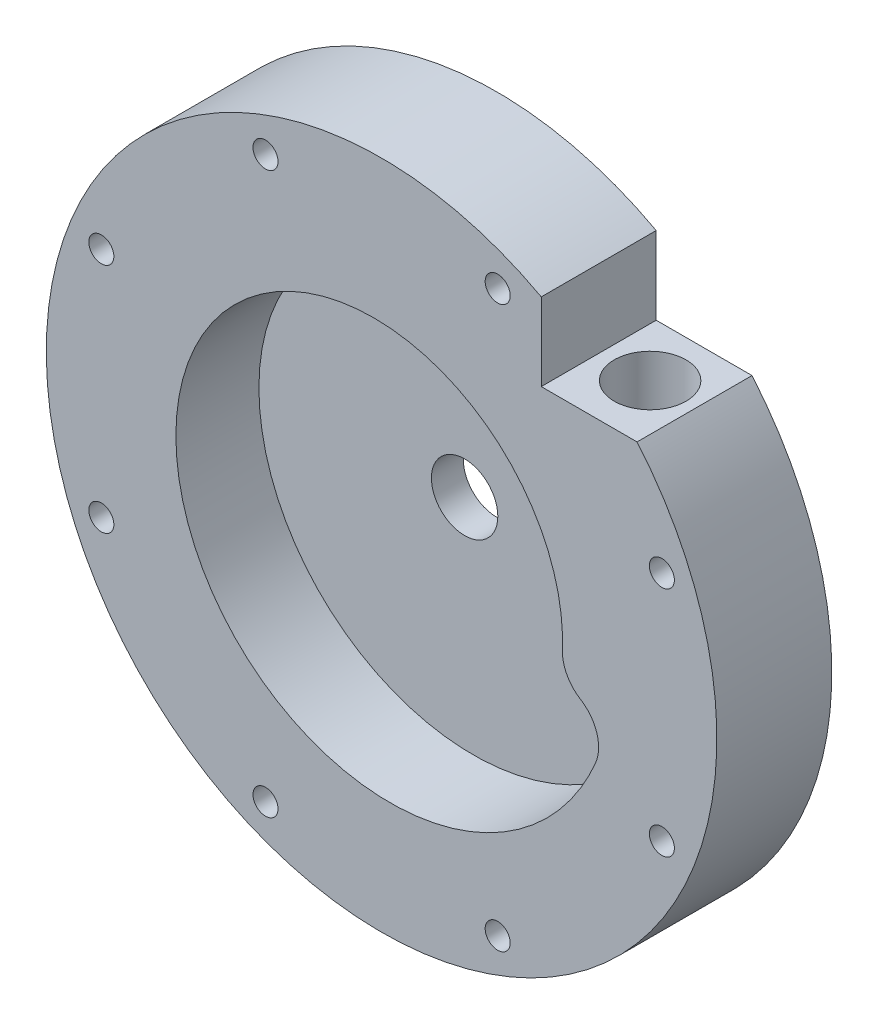
SolidWorks part; units mm, degrees
material "6061-T6 (SS)"
ref_plane "Front Plane" through (0, 0, 0) normal (0, 0, 1) x (1, 0, 0)
ref_plane "Top Plane" through (0, 0, 0) normal (0, 1, 0) x (1, 0, 0)
ref_plane "Right Plane" through (0, 0, 0) normal (1, 0, 0) x (0, 0, -1)
sketch "Sketch22" plane through (0, 0, 0) normal (0, 1, 0) x (1, 0, 0)
  line L0 (-25.4, 0) -> (-6.604, 0)
  line L1 (-25.4, 0) -> (-25.4, -16.51)
  line L2 (-17.4625, 6.35) -> (-17.4625, 3.175)
  line L3 (-25.4, -16.51) -> (-66.675, -16.51)
  line L4 (-66.675, -16.51) -> (-66.675, 6.35)
  line L9 (-17.4625, 6.35) -> (-66.675, 6.35)
  line L10 (0, 0) -> (0, 9.525) construction
  line L11 (-6.604, 6.35) -> (-6.604, 0)
  line L12 (-17.4625, 3.175) -> (-11.1125, 3.175)
  line L15 (-11.1125, 3.175) -> (-11.1125, 6.35)
  line L16 (-11.1125, 6.35) -> (-6.604, 6.35)
  line L17 (-25.4, -0.508) -> (-0.1653, -0.508) construction
  line L18 (-0.1653, -9.508) -> (-0.1653, -0.508) construction
  dimension "D5" = 50.8
  dimension "D6" = 133.35
  dimension "D7" = 13.208
  dimension "D2" = 6.35
  dimension "D4" = 22.225
  dimension "D8" = 3.175
  dimension "D1" = 6.35
  dimension "D3" = 22.86
  dimension "D9" = 0.508
revolve "Main Body" add sketch "Sketch22" angle 360 about L10
curve "Volute Spiral"
  spline degree 3 poles (35.9487, 0, 0) (35.9516, 0.0754, 0) (35.9573, 0.2262, 0) (35.9642, 0.4524, 0) (35.9698, 0.6788, 0) (35.9739, 0.9052, 0) (35.9766, 1.1318, 0) (35.9779, 1.3583, 0) (35.9778, 1.585, 0) (35.9763, 1.8117, 0) (35.9733, 2.0385, 0) (35.969, 2.2653, 0) (35.9632, 2.4921, 0) (35.956, 2.7189, 0) (35.9473, 2.9457, 0) (35.9373, 3.1726, 0) (35.9258, 3.3994, 0) (35.9129, 3.6262, 0) (35.8986, 3.853, 0) (35.8828, 4.0798, 0) (35.8656, 4.3065, 0) (35.847, 4.5331, 0) (35.827, 4.7597, 0) (35.8055, 4.9862, 0) (35.7826, 5.2127, 0) (35.7583, 5.439, 0) (35.7326, 5.6653, 0) (35.7054, 5.8914, 0) (35.6768, 6.1174, 0) (35.6468, 6.3433, 0) (35.6153, 6.5691, 0) (35.5825, 6.7947, 0) (35.5482, 7.0201, 0) (35.5124, 7.2455, 0) (35.4753, 7.4706, 0) (35.4367, 7.6955, 0) (35.3967, 7.9203, 0) (35.3553, 8.1449, 0) (35.3125, 8.3692, 0) (35.2683, 8.5934, 0) (35.2226, 8.8173, 0) (35.1755, 9.041, 0) (35.127, 9.2644, 0) (35.0771, 9.4876, 0) (35.0257, 9.7105, 0) (34.973, 9.9332, 0) (34.9188, 10.1556, 0) (34.8633, 10.3777, 0) (34.8063, 10.5995, 0) (34.7479, 10.821, 0) (34.6881, 11.0422, 0) (34.6269, 11.263, 0) (34.5643, 11.4836, 0) (34.5004, 11.7037, 0) (34.435, 11.9236, 0) (34.3682, 12.1431, 0) (34.3, 12.3622, 0) (34.2304, 12.5809, 0) (34.1594, 12.7993, 0) (34.0871, 13.0172, 0) (34.0133, 13.2348, 0) (33.9382, 13.4519, 0) (33.8617, 13.6686, 0) (33.7838, 13.8849, 0) (33.7045, 14.1008, 0) (33.6238, 14.3162, 0) (33.5418, 14.5311, 0) (33.4584, 14.7456, 0) (33.3737, 14.9596, 0) (33.2875, 15.1732, 0) (33.2, 15.3862, 0) (33.1112, 15.5988, 0) (33.021, 15.8108, 0) (32.9294, 16.0223, 0) (32.8365, 16.2333, 0) (32.7422, 16.4438, 0) (32.6466, 16.6537, 0) (32.5497, 16.8631, 0) (32.4514, 17.0719, 0) (32.3517, 17.2801, 0) (32.2508, 17.4878, 0) (32.1485, 17.6949, 0) (32.0448, 17.9013, 0) (31.9399, 18.1072, 0) (31.8336, 18.3125, 0) (31.7261, 18.5171, 0) (31.6172, 18.7212, 0) (31.507, 18.9246, 0) (31.3955, 19.1273, 0) (31.2827, 19.3294, 0) (31.1685, 19.5308, 0) (31.0531, 19.7316, 0) (30.9365, 19.9317, 0) (30.8185, 20.1311, 0) (30.6992, 20.3298, 0) (30.5787, 20.5278, 0) (30.4569, 20.7251, 0) (30.3338, 20.9217, 0) (30.2094, 21.1175, 0) (30.0838, 21.3126, 0) (29.957, 21.507, 0) (29.8288, 21.7006, 0) (29.6995, 21.8935, 0) (29.5689, 22.0856, 0) (29.437, 22.2769, 0) (29.3039, 22.4674, 0) (29.1696, 22.6571, 0) (29.0341, 22.8461, 0) (28.8973, 23.0342, 0) (28.7593, 23.2215, 0) (28.6201, 23.408, 0) (28.4797, 23.5937, 0) (28.3381, 23.7785, 0) (28.1953, 23.9625, 0) (28.0514, 24.1456, 0) (27.9062, 24.3279, 0) (27.7598, 24.5093, 0) (27.6123, 24.6898, 0) (27.4636, 24.8694, 0) (27.3137, 25.0482, 0) (27.1627, 25.226, 0) (27.0105, 25.403, 0) (26.8572, 25.579, 0) (26.7027, 25.7541, 0) (26.5471, 25.9282, 0) (26.3903, 26.1015, 0) (26.2325, 26.2738, 0) (26.0735, 26.4451, 0) (25.9134, 26.6155, 0) (25.7521, 26.7849, 0) (25.5898, 26.9533, 0) (25.4264, 27.1208, 0) (25.2619, 27.2872, 0) (25.0963, 27.4527, 0) (24.9296, 27.6172, 0) (24.7618, 27.7806, 0) (24.593, 27.9431, 0) (24.4231, 28.1045, 0) (24.2521, 28.2649, 0) (24.0802, 28.4242, 0) (23.9071, 28.5825, 0) (23.733, 28.7398, 0) (23.5579, 28.896, 0) (23.3818, 29.0511, 0) (23.2046, 29.2052, 0) (23.0265, 29.3582, 0) (22.8473, 29.5101, 0) (22.6671, 29.6609, 0) (22.486, 29.8106, 0) (22.3038, 29.9592, 0) (22.1207, 30.1067, 0) (21.9366, 30.2531, 0) (21.7515, 30.3984, 0) (21.5655, 30.5425, 0) (21.3785, 30.6855, 0) (21.1906, 30.8274, 0) (21.0018, 30.9681, 0) (20.812, 31.1076, 0) (20.6213, 31.246, 0) (20.4297, 31.3833, 0) (20.2371, 31.5193, 0) (20.0437, 31.6542, 0) (19.8494, 31.7879, 0) (19.6541, 31.9204, 0) (19.458, 32.0517, 0) (19.2611, 32.1818, 0) (19.0632, 32.3106, 0) (18.8645, 32.4383, 0) (18.665, 32.5648, 0) (18.4646, 32.69, 0) (18.2634, 32.814, 0) (18.0613, 32.9368, 0) (17.8584, 33.0583, 0) (17.6547, 33.1786, 0) (17.4502, 33.2976, 0) (17.2449, 33.4154, 0) (17.0389, 33.5319, 0) (16.832, 33.6471, 0) (16.6244, 33.761, 0) (16.4159, 33.8737, 0) (16.2068, 33.9851, 0) (15.9969, 34.0952, 0) (15.7862, 34.204, 0) (15.5748, 34.3115, 0) (15.3627, 34.4177, 0) (15.1498, 34.5226, 0) (14.9363, 34.6262, 0) (14.722, 34.7285, 0) (14.5071, 34.8294, 0) (14.2914, 34.929, 0) (14.0751, 35.0273, 0) (13.8581, 35.1242, 0) (13.6405, 35.2198, 0) (13.4222, 35.3141, 0) (13.2032, 35.407, 0) (12.9836, 35.4985, 0) (12.7634, 35.5887, 0) (12.5426, 35.6775, 0) (12.3212, 35.765, 0) (12.0991, 35.8511, 0) (11.8765, 35.9358, 0) (11.6532, 36.0191, 0) (11.4294, 36.101, 0) (11.205, 36.1816, 0) (10.9801, 36.2607, 0) (10.7546, 36.3385, 0) (10.5286, 36.4148, 0) (10.302, 36.4898, 0) (10.0749, 36.5633, 0) (9.8473, 36.6355, 0) (9.6192, 36.7062, 0) (9.3906, 36.7755, 0) (9.1615, 36.8434, 0) (8.9319, 36.9098, 0) (8.7018, 36.9748, 0) (8.4713, 37.0384, 0) (8.2403, 37.1006, 0) (8.0089, 37.1613, 0) (7.777, 37.2206, 0) (7.5447, 37.2784, 0) (7.312, 37.3348, 0) (7.0789, 37.3897, 0) (6.8453, 37.4432, 0) (6.6114, 37.4952, 0) (6.3771, 37.5458, 0) (6.1424, 37.5949, 0) (5.9074, 37.6425, 0) (5.672, 37.6887, 0) (5.4362, 37.7334, 0) (5.2002, 37.7766, 0) (4.9637, 37.8183, 0) (4.727, 37.8586, 0) (4.49, 37.8974, 0) (4.2526, 37.9347, 0) (4.015, 37.9705, 0) (3.7771, 38.0048, 0) (3.5389, 38.0377, 0) (3.3004, 38.069, 0) (3.0617, 38.0989, 0) (2.8228, 38.1273, 0) (2.5836, 38.1541, 0) (2.3442, 38.1795, 0) (2.1046, 38.2034, 0) (1.8647, 38.2257, 0) (1.6247, 38.2466, 0) (1.3845, 38.2659, 0) (1.1441, 38.2838, 0) (0.9035, 38.3001, 0) (0.6628, 38.315, 0) (0.4219, 38.3283, 0) (0.1808, 38.3401, 0) (-0.0603, 38.3504, 0) (-0.3016, 38.3591, 0) (-0.543, 38.3664, 0) (-0.7845, 38.3721, 0) (-1.0261, 38.3764, 0) (-1.2677, 38.3791, 0) (-1.5095, 38.3802, 0) (-1.7513, 38.3799, 0) (-1.9932, 38.378, 0) (-2.2351, 38.3746, 0) (-2.477, 38.3697, 0) (-2.719, 38.3633, 0) (-2.961, 38.3554, 0) (-3.203, 38.3459, 0) (-3.445, 38.3349, 0) (-3.687, 38.3223, 0) (-3.929, 38.3083, 0) (-4.1709, 38.2927, 0) (-4.4128, 38.2756, 0) (-4.6546, 38.2569, 0) (-4.8964, 38.2368, 0) (-5.1381, 38.2151, 0) (-5.3798, 38.1919, 0) (-5.6213, 38.1671, 0) (-5.8628, 38.1408, 0) (-6.1041, 38.113, 0) (-6.3453, 38.0837, 0) (-6.5864, 38.0529, 0) (-6.8274, 38.0205, 0) (-7.0682, 37.9866, 0) (-7.3089, 37.9512, 0) (-7.5494, 37.9142, 0) (-7.7897, 37.8758, 0) (-8.0298, 37.8358, 0) (-8.2698, 37.7943, 0) (-8.5095, 37.7512, 0) (-8.749, 37.7067, 0) (-8.9883, 37.6606, 0) (-9.2274, 37.613, 0) (-9.4662, 37.5639, 0) (-9.7048, 37.5133, 0) (-9.9431, 37.4612, 0) (-10.1811, 37.4076, 0) (-10.4189, 37.3524, 0) (-10.6563, 37.2957, 0) (-10.8935, 37.2376, 0) (-11.1303, 37.1779, 0) (-11.3669, 37.1167, 0) (-11.6031, 37.054, 0) (-11.8389, 36.9898, 0) (-12.0745, 36.9241, 0) (-12.3096, 36.857, 0) (-12.5444, 36.7883, 0) (-12.7788, 36.7181, 0) (-13.0129, 36.6464, 0) (-13.2465, 36.5733, 0) (-13.4797, 36.4986, 0) (-13.7126, 36.4225, 0) (-13.9449, 36.3449, 0) (-14.1769, 36.2658, 0) (-14.4084, 36.1852, 0) (-14.6395, 36.1032, 0) (-14.8701, 36.0196, 0) (-15.1002, 35.9346, 0) (-15.3299, 35.8482, 0) (-15.559, 35.7602, 0) (-15.7877, 35.6708, 0) (-16.0159, 35.58, 0) (-16.2435, 35.4877, 0) (-16.4706, 35.3939, 0) (-16.6972, 35.2987, 0) (-16.9232, 35.202, 0) (-17.1487, 35.1039, 0) (-17.3736, 35.0043, 0) (-17.5979, 34.9033, 0) (-17.8217, 34.8009, 0) (-18.0448, 34.697, 0) (-18.2674, 34.5917, 0) (-18.4893, 34.485, 0) (-18.7107, 34.3769, 0) (-18.9314, 34.2673, 0) (-19.1514, 34.1563, 0) (-19.3708, 34.044, 0) (-19.5896, 33.9302, 0) (-19.8077, 33.815, 0) (-20.0251, 33.6984, 0) (-20.2419, 33.5804, 0) (-20.4579, 33.461, 0) (-20.6733, 33.3402, 0) (-20.8879, 33.218, 0) (-21.1018, 33.0945, 0) (-21.315, 32.9696, 0) (-21.5275, 32.8433, 0) (-21.7392, 32.7156, 0) (-21.9501, 32.5866, 0) (-22.1603, 32.4562, 0) (-22.3698, 32.3245, 0) (-22.5784, 32.1914, 0) (-22.7863, 32.057, 0) (-22.9933, 31.9212, 0) (-23.1996, 31.7841, 0) (-23.405, 31.6457, 0) (-23.6097, 31.5059, 0) (-23.8134, 31.3648, 0) (-24.0164, 31.2224, 0) (-24.2185, 31.0787, 0) (-24.4197, 30.9337, 0) (-24.6201, 30.7874, 0) (-24.8196, 30.6398, 0) (-25.0182, 30.4909, 0) (-25.216, 30.3407, 0) (-25.4128, 30.1892, 0) (-25.6087, 30.0365, 0) (-25.8037, 29.8825, 0) (-25.9978, 29.7272, 0) (-26.191, 29.5707, 0) (-26.3832, 29.4129, 0) (-26.5745, 29.2539, 0) (-26.7648, 29.0936, 0) (-26.9541, 28.9321, 0) (-27.1425, 28.7693, 0) (-27.3299, 28.6054, 0) (-27.5163, 28.4402, 0) (-27.7017, 28.2738, 0) (-27.8861, 28.1062, 0) (-28.0695, 27.9374, 0) (-28.2519, 27.7674, 0) (-28.4332, 27.5962, 0) (-28.6135, 27.4238, 0) (-28.7928, 27.2503, 0) (-28.971, 27.0756, 0) (-29.1482, 26.8997, 0) (-29.3243, 26.7227, 0) (-29.4993, 26.5445, 0) (-29.6733, 26.3652, 0) (-29.8461, 26.1847, 0) (-30.0179, 26.0031, 0) (-30.1885, 25.8204, 0) (-30.3581, 25.6366, 0) (-30.5265, 25.4516, 0) (-30.6938, 25.2656, 0) (-30.86, 25.0784, 0) (-31.025, 24.8902, 0) (-31.1889, 24.7009, 0) (-31.3516, 24.5105, 0) (-31.5132, 24.319, 0) (-31.6736, 24.1265, 0) (-31.8329, 23.9329, 0) (-31.9909, 23.7382, 0) (-32.1478, 23.5426, 0) (-32.3034, 23.3459, 0) (-32.4579, 23.1481, 0) (-32.6112, 22.9494, 0) (-32.7632, 22.7496, 0) (-32.914, 22.5489, 0) (-33.0636, 22.3471, 0) (-33.212, 22.1443, 0) (-33.3591, 21.9406, 0) (-33.505, 21.7359, 0) (-33.6496, 21.5302, 0) (-33.7929, 21.3236, 0) (-33.935, 21.116, 0) (-34.0758, 20.9075, 0) (-34.2154, 20.698, 0) (-34.3536, 20.4876, 0) (-34.4906, 20.2763, 0) (-34.6262, 20.0641, 0) (-34.7606, 19.851, 0) (-34.8936, 19.637, 0) (-35.0253, 19.4221, 0) (-35.1557, 19.2063, 0) (-35.2848, 18.9896, 0) (-35.4126, 18.7721, 0) (-35.539, 18.5537, 0) (-35.664, 18.3345, 0) (-35.7877, 18.1144, 0) (-35.9101, 17.8935, 0) (-36.0311, 17.6718, 0) (-36.1507, 17.4493, 0) (-36.2689, 17.2259, 0) (-36.3858, 17.0018, 0) (-36.5013, 16.7769, 0) (-36.6154, 16.5512, 0) (-36.7281, 16.3247, 0) (-36.8394, 16.0975, 0) (-36.9493, 15.8695, 0) (-37.0578, 15.6408, 0) (-37.1649, 15.4113, 0) (-37.2705, 15.1811, 0) (-37.3748, 14.9502, 0) (-37.4776, 14.7186, 0) (-37.5789, 14.4862, 0) (-37.6789, 14.2532, 0) (-37.7773, 14.0195, 0) (-37.8744, 13.7851, 0) (-37.97, 13.5501, 0) (-38.0641, 13.3144, 0) (-38.1567, 13.078, 0) (-38.2479, 12.8411, 0) (-38.3377, 12.6034, 0) (-38.4259, 12.3652, 0) (-38.5127, 12.1264, 0) (-38.598, 11.8869, 0) (-38.6818, 11.6469, 0) (-38.7641, 11.4062, 0) (-38.8449, 11.165, 0) (-38.9242, 10.9233, 0) (-39.002, 10.6809, 0) (-39.0783, 10.4381, 0) (-39.1531, 10.1947, 0) (-39.2264, 9.9507, 0) (-39.2982, 9.7063, 0) (-39.3684, 9.4613, 0) (-39.4371, 9.2159, 0) (-39.5043, 8.9699, 0) (-39.57, 8.7235, 0) (-39.6341, 8.4766, 0) (-39.6966, 8.2292, 0) (-39.7577, 7.9814, 0) (-39.8172, 7.7332, 0) (-39.8751, 7.4845, 0) (-39.9315, 7.2354, 0) (-39.9863, 6.9858, 0) (-40.0396, 6.7359, 0) (-40.0913, 6.4856, 0) (-40.1414, 6.2349, 0) (-40.19, 5.9838, 0) (-40.237, 5.7324, 0) (-40.2825, 5.4806, 0) (-40.3263, 5.2284, 0) (-40.3686, 4.976, 0) (-40.4093, 4.7232, 0) (-40.4484, 4.47, 0) (-40.486, 4.2166, 0) (-40.5219, 3.9629, 0) (-40.5563, 3.7089, 0) (-40.5891, 3.4546, 0) (-40.6203, 3.2001, 0) (-40.6498, 2.9453, 0) (-40.6778, 2.6902, 0) (-40.7042, 2.435, 0) (-40.729, 2.1795, 0) (-40.7522, 1.9237, 0) (-40.7738, 1.6678, 0) (-40.7937, 1.4117, 0) (-40.8121, 1.1554, 0) (-40.8289, 0.8989, 0) (-40.844, 0.6423, 0) (-40.8575, 0.3855, 0) (-40.8695, 0.1285, 0) (-40.8798, -0.1286, 0) (-40.8884, -0.3858, 0) (-40.8955, -0.6431, 0) (-40.901, -0.9005, 0) (-40.9048, -1.158, 0) (-40.907, -1.4156, 0) (-40.9076, -1.6733, 0) (-40.9066, -1.931, 0) (-40.9039, -2.1888, 0) (-40.8996, -2.4467, 0) (-40.8937, -2.7045, 0) (-40.8862, -2.9624, 0) (-40.8771, -3.2203, 0) (-40.8663, -3.4782, 0) (-40.8539, -3.7361, 0) (-40.8399, -3.994, 0) (-40.8242, -4.2519, 0) (-40.8069, -4.5097, 0) (-40.788, -4.7674, 0) (-40.7675, -5.0251, 0) (-40.7453, -5.2828, 0) (-40.7215, -5.5403, 0) (-40.6961, -5.7978, 0) (-40.669, -6.0552, 0) (-40.6404, -6.3124, 0) (-40.6101, -6.5695, 0) (-40.5781, -6.8265, 0) (-40.5446, -7.0834, 0) (-40.5094, -7.3401, 0) (-40.4726, -7.5967, 0) (-40.4342, -7.853, 0) (-40.3941, -8.1092, 0) (-40.3525, -8.3652, 0) (-40.3092, -8.621, 0) (-40.2643, -8.8766, 0) (-40.2177, -9.1319, 0) (-40.1696, -9.3871, 0) (-40.1198, -9.6419, 0) (-40.0684, -9.8966, 0) (-40.0154, -10.1509, 0) (-39.9608, -10.405, 0) (-39.9046, -10.6588, 0) (-39.8468, -10.9123, 0) (-39.7873, -11.1655, 0) (-39.7263, -11.4184, 0) (-39.6636, -11.6709, 0) (-39.5994, -11.9232, 0) (-39.5335, -12.175, 0) (-39.466, -12.4265, 0) (-39.397, -12.6777, 0) (-39.3263, -12.9285, 0) (-39.254, -13.1789, 0) (-39.1802, -13.4288, 0) (-39.1048, -13.6784, 0) (-39.0277, -13.9276, 0) (-38.9491, -14.1763, 0) (-38.8689, -14.4246, 0) (-38.7871, -14.6725, 0) (-38.7038, -14.9199, 0) (-38.6188, -15.1668, 0) (-38.5323, -15.4132, 0) (-38.4442, -15.6592, 0) (-38.3546, -15.9047, 0) (-38.2634, -16.1496, 0) (-38.1706, -16.3941, 0) (-38.0762, -16.638, 0) (-37.9803, -16.8813, 0) (-37.8829, -17.1242, 0) (-37.7839, -17.3664, 0) (-37.6833, -17.6081, 0) (-37.5812, -17.8492, 0) (-37.4776, -18.0898, 0) (-37.3724, -18.3297, 0) (-37.2657, -18.569, 0) (-37.1574, -18.8077, 0) (-37.0477, -19.0458, 0) (-36.9364, -19.2833, 0) (-36.8236, -19.5201, 0) (-36.7092, -19.7562, 0) (-36.5934, -19.9917, 0) (-36.476, -20.2265, 0) (-36.3572, -20.4606, 0) (-36.2368, -20.694, 0) (-36.1149, -20.9268, 0) (-35.9916, -21.1588, 0) (-35.8667, -21.3901, 0) (-35.7404, -21.6206, 0) (-35.6126, -21.8504, 0) (-35.4833, -22.0795, 0) (-35.3526, -22.3078, 0) (-35.2203, -22.5353, 0) (-35.0867, -22.762, 0) (-34.9515, -22.988, 0) (-34.8149, -23.2131, 0) (-34.6769, -23.4375, 0) (-34.5374, -23.661, 0) (-34.3964, -23.8837, 0) (-34.2541, -24.1056, 0) (-34.1103, -24.3266, 0) (-33.9651, -24.5468, 0) (-33.8184, -24.7661, 0) (-33.6704, -24.9845, 0) (-33.5209, -25.202, 0) (-33.3701, -25.4187, 0) (-33.2178, -25.6345, 0) (-33.0641, -25.8493, 0) (-32.9091, -26.0632, 0) (-32.7527, -26.2762, 0) (-32.5949, -26.4883, 0) (-32.4357, -26.6994, 0) (-32.2751, -26.9096, 0) (-32.1132, -27.1188, 0) (-31.95, -27.327, 0) (-31.7854, -27.5343, 0) (-31.6194, -27.7405, 0) (-31.4522, -27.9458, 0) (-31.2835, -28.15, 0) (-31.1136, -28.3533, 0) (-30.9424, -28.5555, 0) (-30.7698, -28.7567, 0) (-30.5959, -28.9568, 0) (-30.4207, -29.1559, 0) (-30.2443, -29.354, 0) (-30.0665, -29.5509, 0) (-29.8875, -29.7468, 0) (-29.7072, -29.9417, 0) (-29.5256, -30.1354, 0) (-29.3428, -30.328, 0) (-29.1587, -30.5195, 0) (-28.9733, -30.7099, 0) (-28.7867, -30.8992, 0) (-28.5989, -31.0874, 0) (-28.4099, -31.2744, 0) (-28.2196, -31.4602, 0) (-28.0281, -31.6449, 0) (-27.8354, -31.8285, 0) (-27.6416, -32.0109, 0) (-27.4465, -32.1921, 0) (-27.2502, -32.3721, 0) (-27.0528, -32.5509, 0) (-26.8542, -32.7285, 0) (-26.6544, -32.9049, 0) (-26.4535, -33.0801, 0) (-26.2514, -33.254, 0) (-26.0482, -33.4267, 0) (-25.8438, -33.5982, 0) (-25.6383, -33.7685, 0) (-25.4317, -33.9374, 0) (-25.224, -34.1052, 0) (-25.0152, -34.2716, 0) (-24.8053, -34.4368, 0) (-24.5943, -34.6007, 0) (-24.3822, -34.7633, 0) (-24.1691, -34.9246, 0) (-23.9549, -35.0846, 0) (-23.7396, -35.2432, 0) (-23.5233, -35.4006, 0) (-23.3059, -35.5566, 0) (-23.0876, -35.7113, 0) (-22.8681, -35.8647, 0) (-22.6477, -36.0167, 0) (-22.4263, -36.1674, 0) (-22.2039, -36.3167, 0) (-21.9804, -36.4646, 0) (-21.756, -36.6112, 0) (-21.5306, -36.7564, 0) (-21.3043, -36.9002, 0) (-21.077, -37.0426, 0) (-20.8488, -37.1836, 0) (-20.6196, -37.3232, 0) (-20.3894, -37.4614, 0) (-20.1584, -37.5981, 0) (-19.9264, -37.7335, 0) (-19.6936, -37.8674, 0) (-19.4598, -37.9999, 0) (-19.2252, -38.1309, 0) (-18.9897, -38.2605, 0) (-18.7533, -38.3886, 0) (-18.516, -38.5153, 0) (-18.2779, -38.6405, 0) (-18.039, -38.7643, 0) (-17.7992, -38.8866, 0) (-17.5586, -39.0073, 0) (-17.3172, -39.1266, 0) (-17.075, -39.2444, 0) (-16.8319, -39.3607, 0) (-16.5881, -39.4755, 0) (-16.3436, -39.5888, 0) (-16.0982, -39.7006, 0) (-15.8521, -39.8109, 0) (-15.6052, -39.9196, 0) (-15.3576, -40.0268, 0) (-15.1093, -40.1325, 0) (-14.8602, -40.2366, 0) (-14.6105, -40.3392, 0) (-14.36, -40.4402, 0) (-14.1088, -40.5397, 0) (-13.857, -40.6377, 0) (-13.6045, -40.734, 0) (-13.3513, -40.8288, 0) (-13.0975, -40.922, 0) (-12.843, -41.0137, 0) (-12.5879, -41.1037, 0) (-12.3321, -41.1922, 0) (-12.0758, -41.2791, 0) (-11.8188, -41.3644, 0) (-11.5613, -41.4481, 0) (-11.3031, -41.5302, 0) (-11.0444, -41.6106, 0) (-10.7851, -41.6895, 0) (-10.5253, -41.7668, 0) (-10.2649, -41.8424, 0) (-10.004, -41.9164, 0) (-9.7426, -41.9888, 0) (-9.4806, -42.0596, 0) (-9.2182, -42.1287, 0) (-8.9552, -42.1962, 0) (-8.6918, -42.262, 0) (-8.4279, -42.3262, 0) (-8.1635, -42.3888, 0) (-7.8987, -42.4497, 0) (-7.6334, -42.509, 0) (-7.3677, -42.5666, 0) (-7.1016, -42.6225, 0) (-6.835, -42.6768, 0) (-6.5681, -42.7294, 0) (-6.3007, -42.7803, 0) (-6.033, -42.8296, 0) (-5.7649, -42.8772, 0) (-5.4965, -42.9231, 0) (-5.2277, -42.9673, 0) (-4.9586, -43.0099, 0) (-4.6891, -43.0508, 0) (-4.4194, -43.0899, 0) (-4.1493, -43.1274, 0) (-3.8789, -43.1632, 0) (-3.6082, -43.1973, 0) (-3.3373, -43.2298, 0) (-3.0661, -43.2605, 0) (-2.7946, -43.2895, 0) (-2.5229, -43.3168, 0) (-2.251, -43.3424, 0) (-1.9788, -43.3663, 0) (-1.7064, -43.3885, 0) (-1.4339, -43.4089, 0) (-1.1611, -43.4277, 0) (-0.8882, -43.4448, 0) (-0.615, -43.4601, 0) (-0.3418, -43.4737, 0) (-0.0684, -43.4856, 0) (0.2052, -43.4958, 0) (0.4789, -43.5043, 0) (0.7527, -43.511, 0) (1.0266, -43.516, 0) (1.3005, -43.5193, 0) (1.5746, -43.5209, 0) (1.8488, -43.5208, 0) (2.123, -43.5189, 0) (2.3972, -43.5153, 0) (2.6715, -43.5099, 0) (2.9458, -43.5029, 0) (3.2201, -43.4941, 0) (3.4945, -43.4836, 0) (3.7688, -43.4713, 0) (4.0431, -43.4574, 0) (4.3174, -43.4417, 0) (4.5917, -43.4242, 0) (4.8659, -43.405, 0) (5.1401, -43.3841, 0) (5.4141, -43.3615, 0) (5.6881, -43.3372, 0) (5.962, -43.3111, 0) (6.2358, -43.2832, 0) (6.5095, -43.2537, 0) (6.7831, -43.2224, 0) (7.0565, -43.1894, 0) (7.3298, -43.1547, 0) (7.6029, -43.1182, 0) (7.8759, -43.08, 0) (8.1486, -43.0401, 0) (8.4212, -42.9984, 0) (8.6936, -42.955, 0) (8.9658, -42.9099, 0) (9.2377, -42.8631, 0) (9.5094, -42.8146, 0) (9.7809, -42.7643, 0) (10.0521, -42.7123, 0) (10.3231, -42.6586, 0) (10.5937, -42.6032, 0) (10.8641, -42.546, 0) (11.1342, -42.4872, 0) (11.4039, -42.4266, 0) (11.6734, -42.3643, 0) (11.9425, -42.3003, 0) (12.2113, -42.2346, 0) (12.4797, -42.1672, 0) (12.7477, -42.0981, 0) (13.0154, -42.0273, 0) (13.2827, -41.9548, 0) (13.5496, -41.8805, 0) (13.8161, -41.8046, 0) (14.0822, -41.727, 0) (14.3478, -41.6477, 0) (14.613, -41.5667, 0) (14.8777, -41.4841, 0) (15.142, -41.3997, 0) (15.4058, -41.3136, 0) (15.6692, -41.2259, 0) (15.932, -41.1365, 0) (16.1943, -41.0454, 0) (16.4562, -40.9527, 0) (16.7174, -40.8583, 0) (16.9782, -40.7622, 0) (17.2384, -40.6644, 0) (17.498, -40.565, 0) (17.7571, -40.4639, 0) (18.0156, -40.3612, 0) (18.2735, -40.2568, 0) (18.5309, -40.1508, 0) (18.7876, -40.0432, 0) (19.0436, -39.9339, 0) (19.2991, -39.8229, 0) (19.5539, -39.7104, 0) (19.808, -39.5962, 0) (20.0615, -39.4803, 0) (20.3144, -39.3629, 0) (20.5665, -39.2438, 0) (20.8179, -39.1231, 0) (21.0687, -39.0008, 0) (21.3187, -38.877, 0) (21.568, -38.7515, 0) (21.8166, -38.6244, 0) (22.0644, -38.4957, 0) (22.3114, -38.3654, 0) (22.5577, -38.2335, 0) (22.8033, -38.1001, 0) (23.048, -37.9651, 0) (23.2919, -37.8285, 0) (23.5351, -37.6903, 0) (23.7774, -37.5506, 0) (24.0189, -37.4094, 0) (24.2595, -37.2665, 0) (24.4993, -37.1222, 0) (24.7383, -36.9762, 0) (24.9764, -36.8288, 0) (25.2136, -36.6798, 0) (25.4499, -36.5293, 0) (25.6854, -36.3773, 0) (25.9199, -36.2237, 0) (26.1535, -36.0687, 0) (26.3862, -35.9121, 0) (26.6179, -35.7541, 0) (26.8487, -35.5945, 0) (27.0786, -35.4335, 0) (27.3075, -35.271, 0) (27.5354, -35.1069, 0) (27.7623, -34.9415, 0) (27.9883, -34.7745, 0) (28.2132, -34.6061, 0) (28.4372, -34.4363, 0) (28.6601, -34.265, 0) (28.882, -34.0923, 0) (29.1028, -33.9181, 0) (29.3226, -33.7425, 0) (29.5413, -33.5655, 0) (29.759, -33.387, 0) (29.9756, -33.2072, 0) (30.1911, -33.0259, 0) (30.4055, -32.8433, 0) (30.6188, -32.6592, 0) (30.831, -32.4738, 0) (31.0421, -32.287, 0) (31.2521, -32.0988, 0) (31.4609, -31.9093, 0) (31.6686, -31.7184, 0) (31.8751, -31.5261, 0) (32.0804, -31.3326, 0) (32.2846, -31.1376, 0) (32.4876, -30.9414, 0) (32.6894, -30.7438, 0) (32.89, -30.5449, 0) (33.0894, -30.3447, 0) (33.2875, -30.1433, 0) (33.4845, -29.9405, 0) (33.6802, -29.7364, 0) (33.8747, -29.5311, 0) (34.0679, -29.3244, 0) (34.2599, -29.1166, 0) (34.4506, -28.9074, 0) (34.64, -28.6971, 0) (34.8281, -28.4855, 0) (35.015, -28.2726, 0) (35.2005, -28.0585, 0) (35.3848, -27.8433, 0) (35.5677, -27.6268, 0) (35.7493, -27.4091, 0) (35.9296, -27.1902, 0) (36.1085, -26.9701, 0) (36.2861, -26.7489, 0) (36.4623, -26.5265, 0) (36.6372, -26.3029, 0) (36.8107, -26.0782, 0) (36.9828, -25.8523, 0) (37.1536, -25.6254, 0) (37.3229, -25.3972, 0) (37.4909, -25.168, 0) (37.6574, -24.9377, 0) (37.8226, -24.7062, 0) (37.9863, -24.4737, 0) (38.1486, -24.2401, 0) (38.3094, -24.0054, 0) (38.4688, -23.7697, 0) (38.6268, -23.5329, 0) (38.7833, -23.295, 0) (38.9383, -23.0561, 0) (39.0919, -22.8162, 0) (39.2439, -22.5753, 0) (39.3945, -22.3333, 0) (39.5437, -22.0904, 0) (39.6913, -21.8465, 0) (39.8374, -21.6015, 0) (39.982, -21.3557, 0) (40.1251, -21.1088, 0) (40.2666, -20.861, 0) (40.4067, -20.6122, 0) (40.5452, -20.3625, 0) (40.6821, -20.1119, 0) (40.8175, -19.8604, 0) (40.9514, -19.6079, 0) (41.0837, -19.3546, 0) (41.2144, -19.1004, 0) (41.3436, -18.8453, 0) (41.4711, -18.5893, 0) (41.5971, -18.3325, 0) (41.7215, -18.0748, 0) (41.8444, -17.8162, 0) (41.9656, -17.5569, 0) (42.0852, -17.2967, 0) (42.2031, -17.0357, 0) (42.3195, -16.7739, 0) (42.4343, -16.5114, 0) (42.5474, -16.248, 0) (42.6589, -15.9839, 0) (42.7687, -15.719, 0) (42.8769, -15.4534, 0) (42.9835, -15.187, 0) (43.0884, -14.9199, 0) (43.1916, -14.6521, 0) (43.2932, -14.3836, 0) (43.3931, -14.1144, 0) (43.4913, -13.8444, 0) (43.5879, -13.5739, 0) (43.6828, -13.3026, 0) (43.776, -13.0307, 0) (43.8675, -12.7581, 0) (43.9573, -12.4849, 0) (44.0454, -12.2111, 0) (44.1318, -11.9367, 0) (44.2164, -11.6617, 0) (44.2994, -11.386, 0) (44.3807, -11.1098, 0) (44.4602, -10.833, 0) (44.538, -10.5557, 0) (44.6141, -10.2778, 0) (44.6884, -9.9994, 0) (44.761, -9.7204, 0) (44.8319, -9.4409, 0) (44.901, -9.1609, 0) (44.9684, -8.8805, 0) (45.034, -8.5995, 0) (45.0979, -8.3181, 0) (45.16, -8.0362, 0) (45.2204, -7.7538, 0) (45.279, -7.471, 0) (45.3358, -7.1878, 0) (45.3908, -6.9041, 0) (45.4441, -6.6201, 0) (45.4956, -6.3356, 0) (45.5453, -6.0508, 0) (45.5932, -5.7656, 0) (45.6394, -5.48, 0) (45.6837, -5.1941, 0) (45.7263, -4.9078, 0) (45.7671, -4.6212, 0) (45.8061, -4.3343, 0) (45.8432, -4.0471, 0) (45.8786, -3.7596, 0) (45.9122, -3.4717, 0) (45.944, -3.1837, 0) (45.9739, -2.8953, 0) (46.0021, -2.6067, 0) (46.0284, -2.3179, 0) (46.053, -2.0288, 0) (46.0757, -1.7396, 0) (46.0966, -1.4501, 0) (46.1157, -1.1604, 0) (46.133, -0.8705, 0) (46.1484, -0.5805, 0) (46.1621, -0.2903, 0) (46.1697, -0.0968, 0) (46.1735, 0, 0) knots 0 0 0 0 0.000879 0.001759 0.002638 0.003518 0.004398 0.005279 0.006159 0.00704 0.007921 0.008802 0.009684 0.010565 0.011447 0.012329 0.013212 0.014094 0.014977 0.01586 0.016744 0.017627 0.018511 0.019395 0.020279 0.021163 0.022048 0.022933 0.023818 0.024703 0.025589 0.026475 0.027361 0.028247 0.029133 0.03002 0.030907 0.031794 0.032681 0.033569 0.034457 0.035345 0.036233 0.037122 0.03801 0.038899 0.039789 0.040678 0.041568 0.042458 0.043348 0.044238 0.045129 0.04602 0.046911 0.047802 0.048693 0.049585 0.050477 0.051369 0.052262 0.053154 0.054047 0.05494 0.055834 0.056727 0.057621 0.058515 0.05941 0.060304 0.061199 0.062094 0.062989 0.063884 0.06478 0.065676 0.066572 0.067469 0.068365 0.069262 0.070159 0.071056 0.071954 0.072852 0.07375 0.074648 0.075546 0.076445 0.077344 0.078243 0.079143 0.080042 0.080942 0.081842 0.082743 0.083643 0.084544 0.085445 0.086346 0.087248 0.08815 0.089052 0.089954 0.090856 0.091759 0.092662 0.093565 0.094468 0.095372 0.096276 0.09718 0.098084 0.098989 0.099894 0.100799 0.101704 0.102609 0.103515 0.104421 0.105327 0.106234 0.10714 0.108047 0.108954 0.109862 0.110769 0.111677 0.112585 0.113494 0.114402 0.115311 0.11622 0.117129 0.118039 0.118948 0.119858 0.120769 0.121679 0.12259 0.123501 0.124412 0.125323 0.126235 0.127147 0.128059 0.128971 0.129884 0.130797 0.13171 0.132623 0.133536 0.13445 0.135364 0.136278 0.137193 0.138108 0.139023 0.139938 0.140853 0.141769 0.142685 0.143601 0.144517 0.145434 0.146351 0.147268 0.148185 0.149103 0.15002 0.150938 0.151857 0.152775 0.153694 0.154613 0.155532 0.156452 0.157371 0.158291 0.159212 0.160132 0.161053 0.161974 0.162895 0.163816 0.164738 0.16566 0.166582 0.167504 0.168427 0.169349 0.170272 0.171196 0.172119 0.173043 0.173967 0.174891 0.175816 0.176741 0.177666 0.178591 0.179516 0.180442 0.181368 0.182294 0.18322 0.184147 0.185074 0.186001 0.186928 0.187856 0.188784 0.189712 0.19064 0.191569 0.192498 0.193427 0.194356 0.195286 0.196215 0.197145 0.198076 0.199006 0.199937 0.200868 0.201799 0.20273 0.203662 0.204594 0.205526 0.206459 0.207391 0.208324 0.209257 0.210191 0.211124 0.212058 0.212992 0.213927 0.214861 0.215796 0.216731 0.217667 0.218602 0.219538 0.220474 0.22141 0.222347 0.223284 0.224221 0.225158 0.226095 0.227033 0.227971 0.228909 0.229848 0.230787 0.231726 0.232665 0.233604 0.234544 0.235484 0.236424 0.237364 0.238305 0.239246 0.240187 0.241128 0.24207 0.243012 0.243954 0.244896 0.245839 0.246782 0.247725 0.248668 0.249612 0.250556 0.2515 0.252444 0.253389 0.254333 0.255278 0.256224 0.257169 0.258115 0.259061 0.260007 0.260954 0.2619 0.262847 0.263795 0.264742 0.26569 0.266638 0.267586 0.268534 0.269483 0.270432 0.271381 0.272331 0.27328 0.27423 0.27518 0.276131 0.277081 0.278032 0.278983 0.279935 0.280886 0.281838 0.28279 0.283743 0.284695 0.285648 0.286601 0.287555 0.288508 0.289462 0.290416 0.29137 0.292325 0.29328 0.294235 0.29519 0.296146 0.297102 0.298058 0.299014 0.29997 0.300927 0.301884 0.302841 0.303799 0.304757 0.305715 0.306673 0.307631 0.30859 0.309549 0.310508 0.311468 0.312428 0.313388 0.314348 0.315308 0.316269 0.31723 0.318191 0.319152 0.320114 0.321076 0.322038 0.323001 0.323963 0.324926 0.325889 0.326853 0.327817 0.32878 0.329745 0.330709 0.331674 0.332639 0.333604 0.334569 0.335535 0.336501 0.337467 0.338433 0.3394 0.340367 0.341334 0.342301 0.343269 0.344237 0.345205 0.346173 0.347142 0.34811 0.34908 0.350049 0.351019 0.351988 0.352958 0.353929 0.354899 0.35587 0.356841 0.357813 0.358784 0.359756 0.360728 0.3617 0.362673 0.363646 0.364619 0.365592 0.366566 0.367539 0.368514 0.369488 0.370462 0.371437 0.372412 0.373388 0.374363 0.375339 0.376315 0.377291 0.378268 0.379245 0.380222 0.381199 0.382176 0.383154 0.384132 0.38511 0.386089 0.387068 0.388047 0.389026 0.390006 0.390985 0.391965 0.392946 0.393926 0.394907 0.395888 0.396869 0.397851 0.398833 0.399815 0.400797 0.401779 0.402762 0.403745 0.404728 0.405712 0.406696 0.40768 0.408664 0.409648 0.410633 0.411618 0.412603 0.413589 0.414575 0.415561 0.416547 0.417534 0.41852 0.419507 0.420495 0.421482 0.42247 0.423458 0.424446 0.425435 0.426423 0.427412 0.428402 0.429391 0.430381 0.431371 0.432361 0.433352 0.434343 0.435334 0.436325 0.437316 0.438308 0.4393 0.440292 0.441285 0.442278 0.443271 0.444264 0.445258 0.446251 0.447245 0.44824 0.449234 0.450229 0.451224 0.452219 0.453215 0.454211 0.455207 0.456203 0.457199 0.458196 0.459193 0.460191 0.461188 0.462186 0.463184 0.464182 0.465181 0.46618 0.467179 0.468178 0.469177 0.470177 0.471177 0.472178 0.473178 0.474179 0.47518 0.476181 0.477183 0.478185 0.479187 0.480189 0.481192 0.482195 0.483198 0.484201 0.485205 0.486209 0.487213 0.488217 0.489222 0.490226 0.491232 0.492237 0.493243 0.494248 0.495255 0.496261 0.497267 0.498274 0.499281 0.500289 0.501297 0.502304 0.503313 0.504321 0.50533 0.506338 0.507348 0.508357 0.509367 0.510377 0.511387 0.512397 0.513408 0.514419 0.51543 0.516441 0.517453 0.518465 0.519477 0.52049 0.521502 0.522515 0.523528 0.524542 0.525556 0.52657 0.527584 0.528598 0.529613 0.530628 0.531643 0.532659 0.533674 0.53469 0.535707 0.536723 0.53774 0.538757 0.539774 0.540792 0.54181 0.542828 0.543846 0.544864 0.545883 0.546902 0.547921 0.548941 0.549961 0.550981 0.552001 0.553022 0.554043 0.555064 0.556085 0.557107 0.558128 0.559151 0.560173 0.561196 0.562218 0.563241 0.564265 0.565288 0.566312 0.567336 0.568361 0.569386 0.57041 0.571436 0.572461 0.573487 0.574513 0.575539 0.576565 0.577592 0.578619 0.579646 0.580673 0.581701 0.582729 0.583757 0.584786 0.585815 0.586844 0.587873 0.588902 0.589932 0.590962 0.591992 0.593023 0.594054 0.595085 0.596116 0.597147 0.598179 0.599211 0.600244 0.601276 0.602309 0.603342 0.604375 0.605409 0.606443 0.607477 0.608511 0.609546 0.610581 0.611616 0.612651 0.613687 0.614723 0.615759 0.616795 0.617832 0.618869 0.619906 0.620943 0.621981 0.623019 0.624057 0.625096 0.626134 0.627173 0.628213 0.629252 0.630292 0.631332 0.632372 0.633413 0.634453 0.635494 0.636536 0.637577 0.638619 0.639661 0.640703 0.641746 0.642789 0.643832 0.644875 0.645919 0.646963 0.648007 0.649051 0.650096 0.651141 0.652186 0.653231 0.654277 0.655323 0.656369 0.657415 0.658462 0.659509 0.660556 0.661604 0.662651 0.663699 0.664748 0.665796 0.666845 0.667894 0.668943 0.669993 0.671042 0.672092 0.673143 0.674193 0.675244 0.676295 0.677346 0.678398 0.67945 0.680502 0.681554 0.682607 0.68366 0.684713 0.685766 0.68682 0.687874 0.688928 0.689982 0.691037 0.692092 0.693147 0.694203 0.695258 0.696314 0.697371 0.698427 0.699484 0.700541 0.701598 0.702656 0.703713 0.704771 0.70583 0.706888 0.707947 0.709006 0.710066 0.711125 0.712185 0.713245 0.714305 0.715366 0.716427 0.717488 0.71855 0.719611 0.720673 0.721735 0.722798 0.72386 0.724923 0.725987 0.72705 0.728114 0.729178 0.730242 0.731307 0.732371 0.733436 0.734502 0.735567 0.736633 0.737699 0.738766 0.739832 0.740899 0.741966 0.743033 0.744101 0.745169 0.746237 0.747306 0.748374 0.749443 0.750512 0.751582 0.752652 0.753722 0.754792 0.755862 0.756933 0.758004 0.759075 0.760147 0.761219 0.762291 0.763363 0.764436 0.765508 0.766582 0.767655 0.768729 0.769802 0.770877 0.771951 0.773026 0.774101 0.775176 0.776251 0.777327 0.778403 0.779479 0.780556 0.781632 0.782709 0.783787 0.784864 0.785942 0.78702 0.788098 0.789177 0.790256 0.791335 0.792414 0.793494 0.794574 0.795654 0.796734 0.797815 0.798896 0.799977 0.801058 0.80214 0.803222 0.804304 0.805387 0.806469 0.807552 0.808636 0.809719 0.810803 0.811887 0.812971 0.814056 0.815141 0.816226 0.817311 0.818397 0.819483 0.820569 0.821655 0.822742 0.823829 0.824916 0.826004 0.827091 0.828179 0.829268 0.830356 0.831445 0.832534 0.833623 0.834713 0.835803 0.836893 0.837983 0.839074 0.840165 0.841256 0.842347 0.843439 0.844531 0.845623 0.846715 0.847808 0.848901 0.849994 0.851088 0.852181 0.853275 0.85437 0.855464 0.856559 0.857654 0.858749 0.859845 0.860941 0.862037 0.863133 0.86423 0.865327 0.866424 0.867521 0.868619 0.869717 0.870815 0.871914 0.873013 0.874112 0.875211 0.87631 0.87741 0.87851 0.879611 0.880711 0.881812 0.882913 0.884014 0.885116 0.886218 0.88732 0.888423 0.889525 0.890628 0.891732 0.892835 0.893939 0.895043 0.896147 0.897252 0.898356 0.899461 0.900567 0.901672 0.902778 0.903884 0.904991 0.906097 0.907204 0.908311 0.909419 0.910527 0.911635 0.912743 0.913851 0.91496 0.916069 0.917178 0.918288 0.919398 0.920508 0.921618 0.922729 0.92384 0.924951 0.926062 0.927174 0.928286 0.929398 0.93051 0.931623 0.932736 0.933849 0.934963 0.936077 0.937191 0.938305 0.93942 0.940534 0.941649 0.942765 0.94388 0.944996 0.946113 0.947229 0.948346 0.949463 0.95058 0.951697 0.952815 0.953933 0.955051 0.95617 0.957289 0.958408 0.959527 0.960647 0.961767 0.962887 0.964007 0.965128 0.966249 0.96737 0.968491 0.969613 0.970735 0.971857 0.97298 0.974103 0.975226 0.976349 0.977473 0.978596 0.979721 0.980845 0.98197 0.983094 0.98422 0.985345 0.986471 0.987597 0.988723 0.98985 0.990976 0.992103 0.993231 0.994358 0.995486 0.996614 0.997742 0.998871 1 1 1 1
sketch "Sketch23" plane through (0, 0, 0) normal (0, 0, 1) x (1, 0, 0)
  arc A9 (39.5526, -6.7699) -> (42.554, -16.2316) centre (35.542, -13.249) cw
  arc A10 (39.5526, -6.7699) -> (35.9487, 0) centre (43.5632, -0.2907) cw
  spline S1 degree 3 poles (2032.2967, -112.9679) (24.3117, -28.1062) (35.5238, -14.0537) (35.9642, 0.4524) (35.9698, 0.6788) (35.978, 1.1318) (35.9808, 2.1906) (35.9203, 3.7799) (35.7473, 5.6682) (35.4899, 7.4743) (35.1415, 9.2689) (34.7024, 11.0474) (34.1734, 12.8052) (33.5555, 14.5378) (32.8499, 16.2406) (32.0579, 17.9093) (31.1812, 19.5395) (30.2217, 21.1268) (29.1814, 22.6671) (28.0626, 24.1562) (26.8679, 25.5901) (25.6, 26.965) (24.2618, 28.2771) (22.8563, 29.5228) (21.3869, 30.6987) (19.8571, 31.8015) (18.2704, 32.828) (16.6307, 33.7754) (14.9419, 34.6409) (13.2081, 35.422) (11.4336, 36.1163) (9.6226, 36.7217) (7.7796, 37.2362) (5.9092, 37.6583) (4.016, 37.9864) (2.1048, 38.2193) (0.1803, 38.3561) (-1.7527, 38.3959) (-3.6892, 38.3382) (-5.6243, 38.1829) (-7.5532, 37.9299) (-9.4708, 37.5794) (-11.3722, 37.132) (-13.2527, 36.5883) (-15.1071, 35.9494) (-16.9308, 35.2164) (-18.719, 34.3909) (-20.467, 33.4746) (-22.1701, 32.4694) (-23.8239, 31.3775) (-25.4239, 30.2014) (-26.9658, 28.9437) (-28.4455, 27.6072) (-29.859, 26.1951) (-31.2023, 24.7106) (-32.4718, 23.1572) (-33.664, 21.5386) (-34.7754, 19.8587) (-35.803, 18.1214) (-36.7437, 16.3309) (-37.5948, 14.4916) (-38.3539, 12.6081) (-39.0185, 10.6848) (-39.5866, 8.7265) (-40.0564, 6.7381) (-40.4263, 4.7245) (-40.6948, 2.6907) (-40.861, 0.6418) (-40.9241, -1.4169) (-40.8833, -3.4804) (-40.7384, -5.5433) (-40.4894, -7.6005) (-40.1364, -9.6466) (-39.68, -11.6765) (-39.1208, -13.6848) (-38.46, -15.6664) (-37.6987, -17.6161) (-36.8386, -19.5288) (-35.8813, -21.3996) (-34.8291, -23.2234) (-33.684, -24.9955) (-32.4488, -26.7111) (-31.1261, -28.3656) (-29.7191, -29.9546) (-28.2309, -31.4738) (-26.665, -32.919) (-25.0251, -34.2863) (-23.3151, -35.5718) (-21.539, -36.772) (-19.7012, -37.8835) (-17.806, -38.9031) (-15.8581, -39.8277) (-13.8621, -40.6548) (-11.8231, -41.3818) (-9.7459, -42.0065) (-7.6359, -42.5268) (-5.4981, -42.9411) (-3.338, -43.2478) (-1.1609, -43.4458) (1.0277, -43.5342) (3.2222, -43.5122) (5.4171, -43.3795) (7.6068, -43.136) (9.7857, -42.782) (11.9482, -42.3178) (14.0887, -41.7442) (16.2017, -41.0623) (18.2818, -40.2733) (20.3235, -39.379) (22.3214, -38.381) (24.2702, -37.2817) (26.165, -36.0833) (28.0005, -34.7886) (29.7719, -33.4005) (31.4745, -31.9221) (33.1036, -30.3569) (34.6549, -28.7085) (36.124, -26.9808) (37.5069, -25.1779) (38.7998, -23.3041) (39.999, -21.3639) (41.1011, -19.362) (42.103, -17.3033) (43.0016, -15.1927) (43.7944, -13.0354) (44.4789, -10.8369) (45.0529, -8.6024) (45.5146, -6.3376) (45.8479, -4.1437) (46.0176, -2.5105) (46.0902, -1.5466) (46.1157, -1.1604) (46.133, -0.8705) (46.1484, -0.5805) (46.9534, 16.4404) (35.9358, 33.8664) (2045.3238, -34.5738) knots -0.166508 -0.166508 -0.166508 -0.166508 0.000879 0.001759 0.002638 0.003518 0.00704 0.014977 0.022048 0.029133 0.036233 0.043348 0.050477 0.057621 0.06478 0.071954 0.079143 0.086346 0.093565 0.100799 0.108047 0.115311 0.12259 0.129884 0.137193 0.144517 0.151857 0.159212 0.166582 0.173967 0.181368 0.188784 0.196215 0.203662 0.211124 0.218602 0.226095 0.233604 0.241128 0.248668 0.256224 0.263795 0.271381 0.278983 0.286601 0.294235 0.301884 0.309549 0.31723 0.324926 0.332639 0.340367 0.34811 0.35587 0.363646 0.371437 0.379245 0.387068 0.394907 0.402762 0.410633 0.41852 0.426423 0.434343 0.442278 0.450229 0.458196 0.46618 0.474179 0.482195 0.490226 0.498274 0.506338 0.514419 0.522515 0.530628 0.538757 0.546902 0.555064 0.563241 0.571436 0.579646 0.587873 0.596116 0.604375 0.612651 0.620943 0.629252 0.637577 0.645919 0.654277 0.662651 0.671042 0.67945 0.687874 0.696314 0.704771 0.713245 0.721735 0.730242 0.738766 0.747306 0.755862 0.764436 0.773026 0.781632 0.790256 0.798896 0.807552 0.816226 0.824916 0.833623 0.842347 0.851088 0.859845 0.868619 0.87741 0.886218 0.895043 0.903884 0.912743 0.921618 0.93051 0.93942 0.948346 0.957289 0.966249 0.975226 0.98422 0.992103 0.994358 0.995486 0.996614 0.997742 0.998871 1.195214 1.195214 1.195214 1.195214 only from (35.9487, 0) to (46.1735, 0) construction
  spline S2 degree 3 poles (35.9487, 0) (35.9516, 0.0754) (35.9573, 0.2262) (35.9642, 0.4524) (35.9698, 0.6788) (35.978, 1.1318) (35.9808, 2.1906) (35.9203, 3.7799) (35.7473, 5.6682) (35.4899, 7.4743) (35.1415, 9.2689) (34.7024, 11.0474) (34.1734, 12.8052) (33.5555, 14.5378) (32.8499, 16.2406) (32.0579, 17.9093) (31.1812, 19.5395) (30.2217, 21.1268) (29.1814, 22.6671) (28.0626, 24.1562) (26.8679, 25.5901) (25.6, 26.965) (24.2618, 28.2771) (22.8563, 29.5228) (21.3869, 30.6987) (19.8571, 31.8015) (18.2704, 32.828) (16.6307, 33.7754) (14.9419, 34.6409) (13.2081, 35.422) (11.4336, 36.1163) (9.6226, 36.7217) (7.7796, 37.2362) (5.9092, 37.6583) (4.016, 37.9864) (2.1048, 38.2193) (0.1803, 38.3561) (-1.7527, 38.3959) (-3.6892, 38.3382) (-5.6243, 38.1829) (-7.5532, 37.9299) (-9.4708, 37.5794) (-11.3722, 37.132) (-13.2527, 36.5883) (-15.1071, 35.9494) (-16.9308, 35.2164) (-18.719, 34.3909) (-20.467, 33.4746) (-22.1701, 32.4694) (-23.8239, 31.3775) (-25.4239, 30.2014) (-26.9658, 28.9437) (-28.4455, 27.6072) (-29.859, 26.1951) (-31.2023, 24.7106) (-32.4718, 23.1572) (-33.664, 21.5386) (-34.7754, 19.8587) (-35.803, 18.1214) (-36.7437, 16.3309) (-37.5948, 14.4916) (-38.3539, 12.6081) (-39.0185, 10.6848) (-39.5866, 8.7265) (-40.0564, 6.7381) (-40.4263, 4.7245) (-40.6948, 2.6907) (-40.861, 0.6418) (-40.9241, -1.4169) (-40.8833, -3.4804) (-40.7384, -5.5433) (-40.4894, -7.6005) (-40.1364, -9.6466) (-39.68, -11.6765) (-39.1208, -13.6848) (-38.46, -15.6664) (-37.6987, -17.6161) (-36.8386, -19.5288) (-35.8813, -21.3996) (-34.8291, -23.2234) (-33.684, -24.9955) (-32.4488, -26.7111) (-31.1261, -28.3656) (-29.7191, -29.9546) (-28.2309, -31.4738) (-26.665, -32.919) (-25.0251, -34.2863) (-23.3151, -35.5718) (-21.539, -36.772) (-19.7012, -37.8835) (-17.806, -38.9031) (-15.8581, -39.8277) (-13.8621, -40.6548) (-11.8231, -41.3818) (-9.7459, -42.0065) (-7.6359, -42.5268) (-5.4981, -42.9411) (-3.338, -43.2478) (-1.1609, -43.4458) (1.0277, -43.5342) (3.2222, -43.5122) (5.4171, -43.3795) (7.6068, -43.136) (9.7857, -42.782) (11.9482, -42.3178) (14.0887, -41.7442) (16.2017, -41.0623) (18.2818, -40.2733) (20.3235, -39.379) (22.3214, -38.381) (24.2702, -37.2817) (26.165, -36.0833) (28.0005, -34.7886) (29.7719, -33.4005) (31.4745, -31.9221) (33.1036, -30.3569) (34.6549, -28.7085) (36.124, -26.9808) (37.5069, -25.1779) (38.7998, -23.3041) (39.999, -21.3639) (41.1011, -19.362) (42.103, -17.3033) (43.0016, -15.1927) (43.7944, -13.0354) (44.4789, -10.8369) (45.0529, -8.6024) (45.5146, -6.3376) (45.8479, -4.1437) (46.0176, -2.5105) (46.0902, -1.5466) (46.1157, -1.1604) (46.133, -0.8705) (46.1484, -0.5805) (46.1621, -0.2903) (46.1697, -0.0968) (46.1735, 0) knots 0 0 0 0 0.000879 0.001759 0.002638 0.003518 0.00704 0.014977 0.022048 0.029133 0.036233 0.043348 0.050477 0.057621 0.06478 0.071954 0.079143 0.086346 0.093565 0.100799 0.108047 0.115311 0.12259 0.129884 0.137193 0.144517 0.151857 0.159212 0.166582 0.173967 0.181368 0.188784 0.196215 0.203662 0.211124 0.218602 0.226095 0.233604 0.241128 0.248668 0.256224 0.263795 0.271381 0.278983 0.286601 0.294235 0.301884 0.309549 0.31723 0.324926 0.332639 0.340367 0.34811 0.35587 0.363646 0.371437 0.379245 0.387068 0.394907 0.402762 0.410633 0.41852 0.426423 0.434343 0.442278 0.450229 0.458196 0.46618 0.474179 0.482195 0.490226 0.498274 0.506338 0.514419 0.522515 0.530628 0.538757 0.546902 0.555064 0.563241 0.571436 0.579646 0.587873 0.596116 0.604375 0.612651 0.620943 0.629252 0.637577 0.645919 0.654277 0.662651 0.671042 0.67945 0.687874 0.696314 0.704771 0.713245 0.721735 0.730242 0.738766 0.747306 0.755862 0.764436 0.773026 0.781632 0.790256 0.798896 0.807552 0.816226 0.824916 0.833623 0.842347 0.851088 0.859845 0.868619 0.87741 0.886218 0.895043 0.903884 0.912743 0.921618 0.93051 0.93942 0.948346 0.957289 0.966249 0.975226 0.98422 0.992103 0.994358 0.995486 0.996614 0.997742 0.998871 1 1 1 1
  dimension "D1" = 7.62
extrude "Volute Cut" cut sketch "Sketch23" along normal through all
sketch "Sketch28" plane through (0, 0, 16.51) normal (0, 0, 1) x (1, 0, 0)
  line L1 (31.75, 58.6301) -> (50.804, 58.6301)
  line L2 (31.75, 58.6301) -> (31.75, 43.18)
  line L3 (31.75, 43.18) -> (50.804, 43.18)
  line L4 (50.804, 58.6301) -> (50.804, 43.18)
  circle A1 centre (0, 0) radius 66.675 construction
  dimension "D1" = 43.18
  dimension "D2" = 31.75
extrude "Outlet Hole Cut" cut sketch "Sketch28" against normal through all
hole_wizard "Outlet Hole" positions "3DSketch2" profile "Sketch20" hole size "W" standard "ANSI Inch"
sketch3d "3DSketch2"
  line L1 (0, 0, 0) -> (41.529, 0, 0) construction
  line L2 (41.529, 0, 0) -> (41.529, 0, 9.2753) construction
  point P22 (41.529, 43.18, 4.6377)
  point P70 (41.529, 0, 4.6377)
  dimension "D1" = 9.2753
  dimension "D2" = 41.529
sketch "Sketch20" plane through (41.529, 43.18, 4.6377) normal (1, 0, 0) x (0, 0, 1)
  line L0 (0, 0) -> (0, 58.8255)
  line L1 (0, 58.8255) -> (4.9022, 55.88)
  line L2 (4.9022, 55.88) -> (4.9022, 0)
  line L5 (4.9022, 0) -> (0, 0)
  line L10 (0, 58.8255) -> (-4.9022, 55.88) construction
  line L11 (0, -6.35) -> (0, 107.95) construction
  dimension "Hole Dia." = 9.8044
  dimension "Hole Depth" = 55.88
  dimension "Drill Angle" = 118
hole_wizard "Outlet NPT" positions "3DSketch4" profile "Sketch29" hole size "3/8" standard "ANSI Inch"
sketch3d "3DSketch4"
  circle A0 centre (41.529, 43.18, 4.6377) radius 4.9022 construction
  point P0 (41.529, 43.18, 4.6377)
  point P6 (41.529, 48.0822, 4.6377)
sketch "Sketch29" plane through (41.529, 43.18, 4.6377) normal (1, 0, 0) x (0, 0, 1)
  line L0 (0, 0) -> (0, 16.9886)
  line L1 (0, 16.9886) -> (7.1374, 12.7)
  line L2 (7.1374, 12.7) -> (7.1374, 0)
  line L5 (7.1374, 0) -> (0, 0)
  line L10 (0, 16.9886) -> (-7.1374, 12.7) construction
  line L11 (0, -6.35) -> (0, 107.95) construction
  dimension "Hole Dia." = 14.2748
  dimension "Hole Depth" = 12.7
  dimension "Drill Angle" = 118
hole_wizard "Fastener Holes" positions "3DSketch5" profile "Sketch30" hole size "#10" standard "ANSI Inch" end condition through all
sketch3d "3DSketch5"
  line L0 (0, 0, 0) -> (0, 0, 16.51) construction
  line L1 (0, 0, 16.51) -> (66.675, 0, 16.51) construction
  line L3 (0, 0, 16.51) -> (55.733, -23.0854, 16.51) construction
  circle A0 centre (0, 0, 16.51) radius 66.675 construction
  point P0 (55.733, -23.0854, 16.51)
  point P15 (0, 0, 83.185)
  dimension "D1" = 22.5
  dimension "D2" = 60.325
sketch "Sketch30" plane through (55.733, -23.0854, 16.51) normal (1, 0, 0) x (0, -1, 0)
  line L0 (0, 0) -> (0, 22.86)
  line L1 (0, 22.86) -> (2.4892, 22.86)
  line L2 (2.4892, 22.86) -> (2.4892, 0)
  line L5 (2.4892, 0) -> (0, 0)
  line L11 (0, -6.35) -> (0, 107.95) construction
  dimension "Thru Hole Dia." = 4.9784
  dimension "Thru Hole Depth" = 22.86
pattern_circular "CirPattern1" count 8 over 360 about axis through (0, 0, 0) along (0, 0, 1) of "Fastener Holes"
equation "\"D9@Sketch22\"=\"Fluid Clearance@[TP] [Pump] [Ox] Pump.Assembly\""
equation "\"D1@Sketch22\"=\"Volute Floor Thickness@[TP] [Pump] [Ox] Pump.Assembly\""
equation "\"D6@Sketch22\"=\"Casing OD@[TP] [Pump] [Ox] Pump.Assembly\""
equation "\"D3@Sketch22\" = \"Volute Casing Height@[TP] [Pump] [Ox] Pump.Assembly\""
equation "\"D1\" = \"Volute Height@[TP] [Pump] [Ox] Pump.Assembly\""
equation "\"D2\" = \"Outlet Radial Position@[TP] [Pump] [Ox] Pump.Assembly\""
